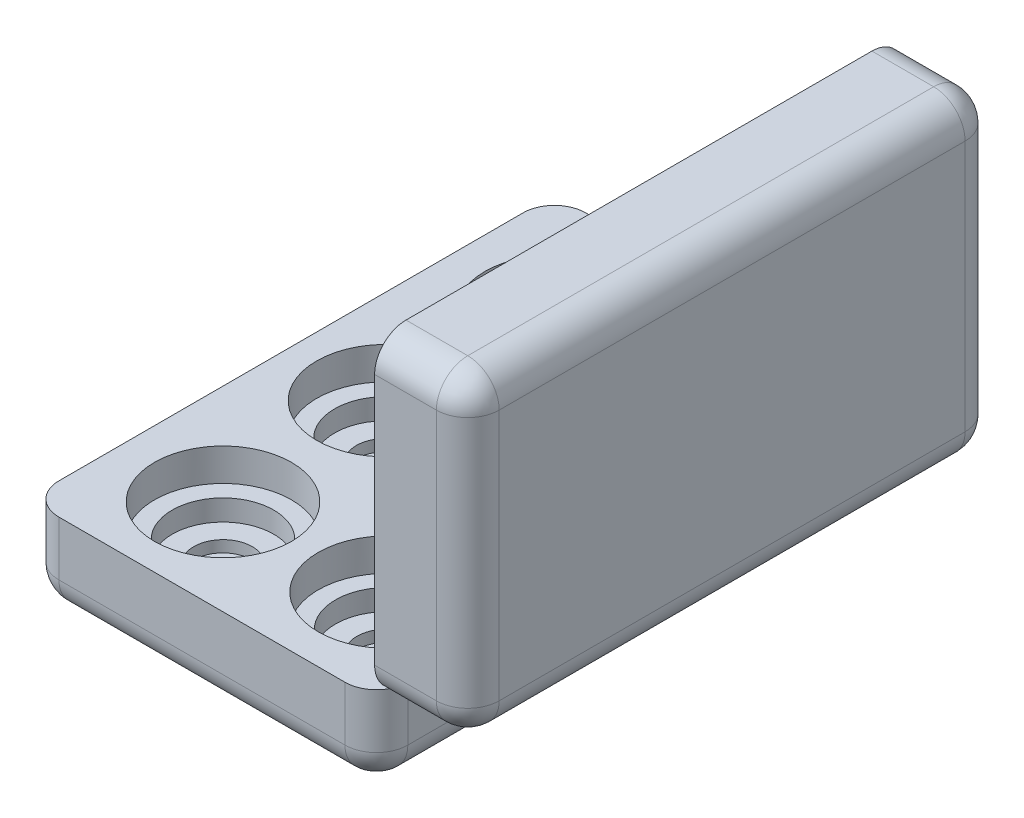
SolidWorks part; units mm, degrees
ref_plane "Front Plane" through (0, 0, 0) normal (0, 0, 1) x (1, 0, 0)
ref_plane "Top Plane" through (0, 0, 0) normal (0, 1, 0) x (1, 0, 0)
ref_plane "Right Plane" through (0, 0, 0) normal (1, 0, 0) x (0, 0, -1)
sketch "Sketch1" plane through (0, 0, 0) normal (0, 1, 0) x (1, 0, 0)
  line L1 (-45.2036, -75.0848) -> (39.4473, -75.0848)
  line L2 (-45.2036, -75.0848) -> (-45.2036, 52.7571)
  line L3 (-45.2036, 52.7571) -> (39.4473, 52.7571)
  line L4 (39.4473, -75.0848) -> (39.4473, 52.7571)
  circle A10 centre (-22.4317, -11.0005) radius 16.706
  circle A17 centre (17.9938, -51.035) radius 16.706
  circle A18 centre (-20.875, -51.9875) radius 16.6212
  circle A19 centre (17.4572, 28.7477) radius 16.706
  circle A20 centre (17.8149, -10.607) radius 16.706
  circle A21 centre (-20.8242, 28.211) radius 16.706
extrude "Boss-Extrude3" add sketch "Sketch1" along normal blind 20.828 contours A21 | L2 L1 L4 L3 | A19 | A20 | A10 | A18 | A17
sketch "Sketch3" plane through (0, 0, 0) normal (0, -1, 0) x (1, 0, 0)
  line L1 (-45.2036, 75.0848) -> (39.4473, 75.0848)
  line L2 (-45.2036, 75.0848) -> (-45.2036, -52.7571)
  line L3 (-45.2036, -52.7571) -> (39.4473, -52.7571)
  line L4 (39.4473, 75.0848) -> (39.4473, -52.7571)
extrude "Boss-Extrude4" add sketch "Sketch3" against normal blind 12.954
sketch "Sketch4" plane through (0, 12.954, 0) normal (0, 1, 0) x (1, 0, 0)
  circle A0 centre (17.8149, -10.607) radius 12.5408
  circle A1 centre (17.4572, 28.7477) radius 12.5263
  circle A2 centre (-20.8242, 28.211) radius 12.5647
  circle A3 centre (-20.875, -51.9875) radius 12.325
  circle A4 centre (-22.4317, -11.0005) radius 12.3324
  circle A5 centre (17.9938, -51.035) radius 12.5125
extrude "Cut-Extrude1" cut sketch "Sketch4" against normal blind 5.08
sketch "Sketch5" plane through (0, 7.874, 0) normal (0, 1, 0) x (1, 0, 0)
  circle A0 centre (-20.8242, 28.211) radius 7.1745
  circle A1 centre (17.8149, -10.607) radius 7.1616
  circle A2 centre (17.4572, 28.7477) radius 7.0517
  circle A3 centre (-22.4317, -11.0005) radius 7.0766
  circle A4 centre (-20.875, -51.9875) radius 7.1052
  circle A5 centre (17.9938, -51.035) radius 7.3359
extrude "Cut-Extrude2" cut sketch "Sketch5" against normal blind 2.794
fillet "Fillet4" radius 7.62 4 edges at (39.4473, 10.414, -52.7571) (-45.2036, 10.414, -52.7571) (-45.2036, 10.414, 75.0848) (39.4473, 10.414, 75.0848)
fillet "Fillet5" radius 7.62 8 edges at (-42.9717, 0, -50.5253) (-45.2036, 0, 11.1638) (-42.9717, 0, 72.8529) (-2.8781, 0, 75.0848) (37.2155, 0, 72.8529) (39.4473, 0, 11.1638) (37.2155, 0, -50.5253) (-2.8781, 0, -52.7571)
sketch "Sketch6" plane through (39.4473, 0, 0) normal (1, 0, 0) x (0, 0, -1)
  line L1 (52.7571, 20.828) -> (-75.5216, 20.828)
  line L2 (52.7571, 20.828) -> (52.7571, 97.1519)
  line L3 (52.7571, 97.1519) -> (-75.5216, 97.1519)
  line L4 (-75.5216, 20.828) -> (-75.5216, 97.1519)
extrude "Boss-Extrude5" add sketch "Sketch6" along normal blind 22.606 separate body
fillet "Fillet6" radius 7.62 8 edges at (62.0533, 20.828, 11.3822) (62.0533, 58.99, 75.5216) (62.0533, 97.1519, 11.3822) (62.0533, 58.99, -52.7571) (50.7503, 20.828, 75.5216) (50.7503, 20.828, -52.7571) (50.7503, 97.1519, -52.7571) (50.7503, 97.1519, 75.5216)
shell "Shell1" thickness 2.54
